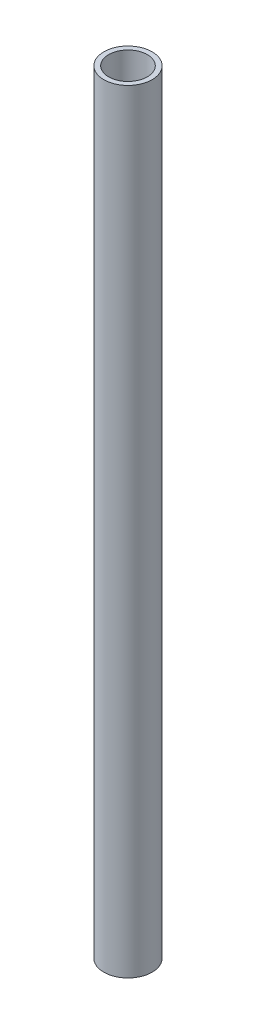
SolidWorks part; units mm, degrees
ref_plane "Front Plane" through (0, 0, 0) normal (0, 0, 1) x (1, 0, 0)
ref_plane "Top Plane" through (0, 0, 0) normal (0, 1, 0) x (1, 0, 0)
ref_plane "Right Plane" through (0, 0, 0) normal (1, 0, 0) x (0, 0, -1)
sketch "Sketch1" plane through (0, 0, 0) normal (0, 1, 0) x (1, 0, 0)
  circle A0 centre (0, 0) radius 4.7625
  circle A1 centre (0, 0) radius 3.81
  dimension "D1" = 9.525
  dimension "D2" = 7.62
extrude "Boss-Extrude1" add sketch "Sketch1" along normal blind 152.4
